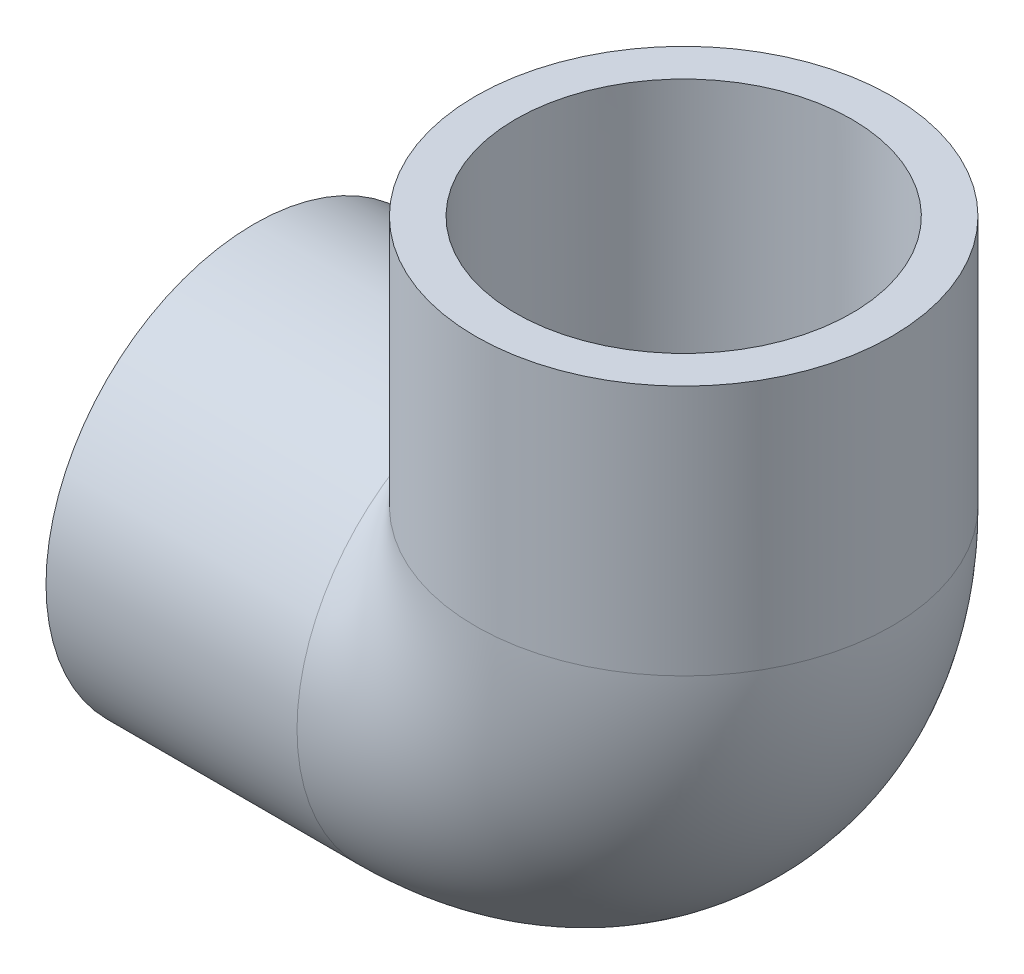
SolidWorks part; units mm, degrees
ref_plane "Front Plane" through (0, 0, 0) normal (0, 0, 1) x (1, 0, 0)
ref_plane "Top Plane" through (0, 0, 0) normal (0, 1, 0) x (1, 0, 0)
ref_plane "Right Plane" through (0, 0, 0) normal (1, 0, 0) x (0, 0, -1)
sketch "Sketch0" plane through (0, 0, 0) normal (0, 0, 1) x (1, 0, 0)
  line L0 (-34.3408, 0) -> (0, 0) construction
  line L1 (0, 0) -> (0, 34.3408) construction
  line L2 (-14.2748, 0) -> (0, 0) construction
  line L3 (0, 0) -> (0, 14.2748) construction
  line L4 (-34.3408, 16.637) -> (-34.3408, -16.637) construction
  line L5 (-14.2748, 13.2842) -> (-34.3408, 13.4366) construction
  line L6 (-14.2748, 13.2842) -> (-14.2748, -13.2842) construction
  line L7 (-14.2748, -13.2842) -> (-34.3408, -13.4366) construction
  line L8 (-34.3408, 13.4366) -> (-34.3408, -13.4366) construction
  line L9 (-16.637, 34.3408) -> (16.637, 34.3408) construction
  line L10 (-13.4366, 34.3408) -> (13.4366, 34.3408) construction
  line L11 (13.4366, 34.3408) -> (13.2842, 14.2748) construction
  line L12 (13.2842, 14.2748) -> (-13.2842, 14.2748) construction
  line L13 (-13.2842, 14.2748) -> (-13.4366, 34.3408) construction
  line L14 (-14.2748, 10.4648) -> (-14.2748, -10.4648) construction
  line L18 (-10.4648, 14.2748) -> (10.4648, 14.2748) construction
  dimension "H" = 34.3408
  dimension "G" = 14.2748
  dimension "M" = 33.274
  dimension "OD A" = 26.8732
  dimension "OD B" = 26.5684
  dimension "ID" = 20.9296
sketch "Sketch1" plane through (0, 0, 0) normal (0, 0, 1) x (1, 0, 0)
  line L0 (-34.3408, 0) -> (0, 0) construction
  line L1 (-34.3408, 0) -> (0, 0) construction
  line L3 (-34.3408, -16.637) -> (-14.2748, -16.637)
  line L4 (-34.3408, -16.637) -> (-34.3408, -13.4366)
  line L5 (-34.3408, -13.4366) -> (-14.2748, -13.2842)
  line L6 (-14.2748, -16.637) -> (-14.2748, -13.2842)
revolve "Revolve1" add sketch "Sketch1" angle 360 about L1
sketch "Sketch2" plane through (0, 0, 0) normal (0, 0, 1) x (1, 0, 0)
  line L0 (13.4366, 34.3408) -> (13.2842, 14.2748)
  line L1 (13.2842, 14.2748) -> (16.637, 14.2748)
  line L2 (16.637, 14.2748) -> (16.637, 34.3408)
  line L3 (16.637, 34.3408) -> (13.4366, 34.3408)
  line L4 (0, 0) -> (0, 34.3408) construction
  line L5 (0, 0) -> (0, 34.3408) construction
revolve "Revolve2" add sketch "Sketch2" angle 360 about L5
sketch "Sketch3" plane through (-14.2748, 0, 0) normal (1, 0, 0) x (0, 0, -1)
  circle A0 centre (0, 0) radius 10.4648
  circle A1 centre (0, 0) radius 16.637
sketch "Sketch4" plane through (0, 0, 0) normal (0, 0, 1) x (1, 0, 0)
  line L0 (-34.3408, 0) -> (0, 0) construction
  line L1 (0, 0) -> (0, 34.3408) construction
  line L2 (-34.3408, 0) -> (-14.2748, 0) construction
  line L3 (0, 14.2748) -> (0, 34.3408) construction
  arc A0 (-14.2748, 0) -> (0, 14.2748) centre (-14.2748, 14.2748) ccw
sweep "Sweep1" add profiles "Sketch3" path "Sketch4"
